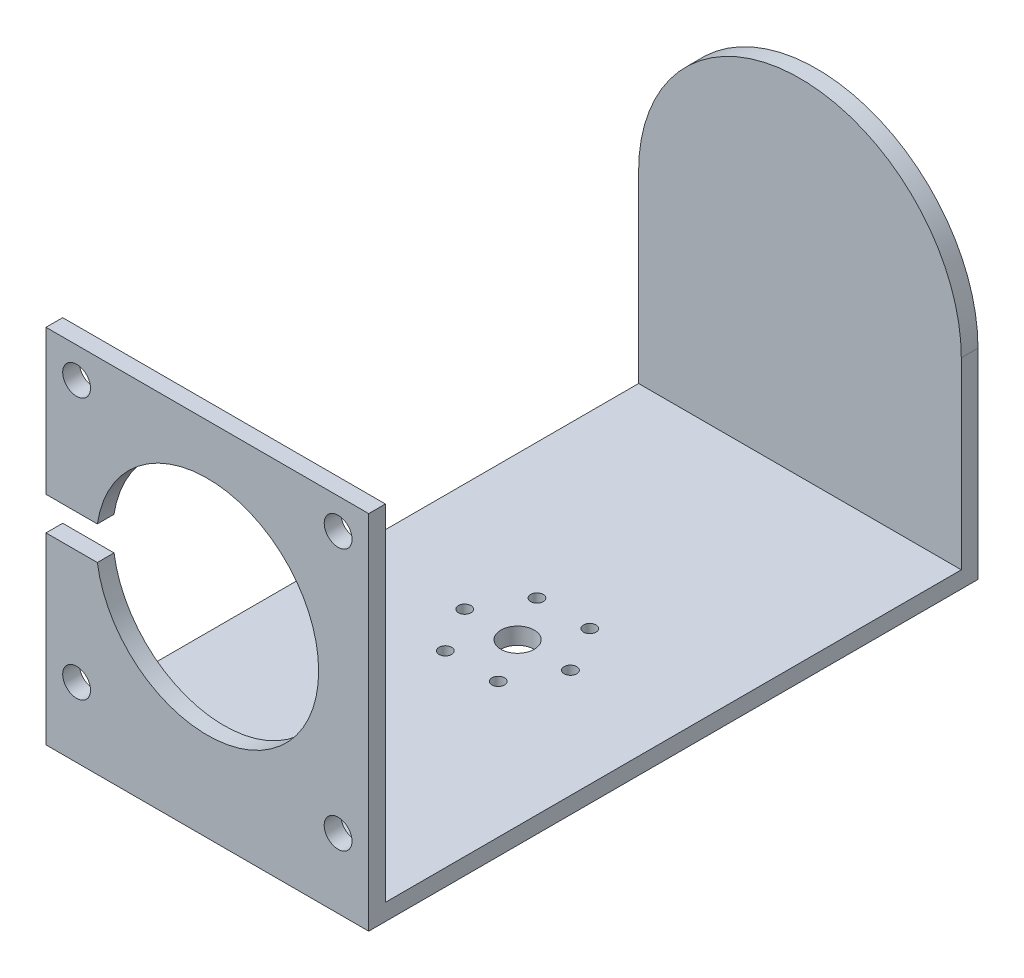
SolidWorks part; units mm, degrees
material "1060 Alloy"
ref_plane "Front Plane" through (0, 0, 0) normal (0, 0, 1) x (1, 0, 0)
ref_plane "Top Plane" through (0, 0, 0) normal (0, 1, 0) x (1, 0, 0)
ref_plane "Right Plane" through (0, 0, 0) normal (1, 0, 0) x (0, 0, -1)
sketch "Sketch1" plane through (0, 0, 0) normal (1, 0, 0) x (0, 0, -1)
  line L0 (-73.3517, 30.4008) -> (-73.3517, -29.5992)
  line L1 (-73.3517, -29.5992) -> (30.1483, -29.5992)
  line L2 (30.1483, -29.5992) -> (30.1483, 30.4008)
  line L3 (30.1483, 30.4008) -> (33.1483, 30.4008)
  line L4 (33.1483, 30.4008) -> (33.1483, -34.5992)
  line L5 (33.1483, -34.5992) -> (-76.3517, -34.5992)
  line L6 (-76.3517, -34.5992) -> (-76.3517, 30.4008)
  line L7 (-76.3517, 30.4008) -> (-73.3517, 30.4008)
  dimension "D1" = 60
  dimension "D2" = 103.5
  dimension "D3" = 3
  dimension "D4" = 65
  dimension "D5" = 109.5
extrude "Boss-Extrude1" add sketch "Sketch1" along normal blind 58
sketch "Sketch2" plane through (0, 0, 76.3517) normal (0, 0, 1) x (1, 0, 0)
  line L0 (0, 30.4008) -> (0, 24.9008) construction
  line L1 (0, 30.4008) -> (0, -34.5992) construction
  line L2 (0, 24.9008) -> (5.5, 24.9008) construction
  line L3 (29, 30.4008) -> (29, -34.5992) construction
  line L4 (58, 30.4008) -> (0, 30.4008) construction
  line L5 (58, -34.5992) -> (0, -34.5992) construction
  line L6 (58, 30.4008) -> (58, 1.4008) construction
  line L7 (58, 30.4008) -> (58, -34.5992) construction
  line L8 (58, 1.4008) -> (0, 1.4008) construction
  circle A0 centre (5.5, 24.9008) radius 2.5
  circle A1 centre (52.5, 24.9008) radius 2.5
  circle A2 centre (52.5, -22.0992) radius 2.5
  circle A3 centre (5.5, -22.0992) radius 2.5
  circle A4 centre (29, 1.4008) radius 20
  dimension "D4" = 5
  dimension "D5" = 40
  dimension "D1" = 5.5
  dimension "D2" = 5.5
  dimension "D3" = 29
extrude "Cut-Extrude1" cut sketch "Sketch2" against normal blind 58
sketch "Sketch3" plane through (0, 0, -33.1483) normal (0, 0, -1) x (-1, 0, 0)
  line L0 (-29, 30.4008) -> (-58, 30.4008)
  line L1 (-58, 30.4008) -> (0, 30.4008) construction
  line L2 (-58, 30.4008) -> (-58, 1.4008)
  line L3 (-58, -34.5992) -> (-58, 30.4008) construction
  arc A0 (-58, 1.4008) -> (-29, 30.4008) centre (-29, 1.4008) cw
  dimension "D1" = 29
extrude "Cut-Extrude2" cut sketch "Sketch3" against normal blind 58
sketch "Sketch4" plane through (0, 0, -33.1483) normal (0, 0, -1) x (-1, 0, 0)
  line L0 (-29, 30.4008) -> (0, 30.4008)
  line L1 (-29, 30.4008) -> (0, 30.4008) construction
  line L2 (0, 30.4008) -> (0, 1.4008)
  line L3 (0, -34.5992) -> (0, 30.4008) construction
  arc A0 (0, 1.4008) -> (-29, 30.4008) centre (-29, 1.4008) ccw
  arc A1 (-29, 30.4008) -> (-58, 1.4008) centre (-29, 1.4008) ccw construction
  dimension "D1" = 29
extrude "Cut-Extrude3" cut sketch "Sketch4" against normal blind 58
sketch "Sketch5" plane through (0, 0, -33.1483) normal (0, 0, -1) x (-1, 0, 0)
  circle A0 centre (-29, 1.4008) radius 2.95
  dimension "D1" = 5.9
extrude "Boss-Extrude2" add sketch "Sketch5" along normal blind 8
sketch "Sketch7" plane through (0, 0, 76.3517) normal (0, 0, 1) x (1, 0, 0)
  line L0 (29, 1.4008) -> (29, 4.4008) construction
  line L1 (29, 4.4008) -> (0, 4.4008)
  line L2 (0, 30.4008) -> (0, -34.5992) construction
  line L3 (29, 4.4008) -> (29, -1.5992)
  line L4 (29, -1.5992) -> (0, -1.5992)
  line L5 (0, -1.5992) -> (0, 4.4008)
  dimension "D1" = 3
  dimension "D2" = 6
extrude "Cut-Extrude5" cut sketch "Sketch7" against normal blind 10
sketch "Sketch13" plane through (0, -34.5992, 0) normal (0, -1, 0) x (-1, 0, 0)
  line L0 (-29, 33.1483) -> (-29, -20.6017) construction
  line L1 (-58, 33.1483) -> (0, 33.1483) construction
  dimension "D1" = 53.75
sketch "Sketch18" plane through (34.226, -34.5992, 37.4771) normal (0, -1, 0) x (-1, 0, 0)
  line L0 (5.226, 16.8754) -> (14.726, 16.8754) construction
  circle A0 centre (5.226, 16.8754) radius 9.5
  dimension "D1" = 19
hole_wizard "#4-40 Tapped Hole4" positions "Sketch24" profile "Sketch23" tap size "#4-40" standard "ANSI Inch"
sketch "Sketch24" plane through (0, -34.5992, 0) normal (0, -1, 0) x (-1, 0, 0)
  point P0 (-19.5, -20.6017)
  point P8 (-24.25, -28.8289)
  point P9 (-33.75, -28.8289)
  point P10 (-38.5, -20.6017)
  point P11 (-33.75, -12.3744)
  point P12 (-24.25, -12.3744)
  dimension "D1" = 6
sketch "Sketch23" plane through (19.5, -34.5992, 20.6017) normal (1, 0, 0) x (0, 0, -1)
  line L0 (0, 0) -> (0, 8.2792)
  line L1 (0, 8.2792) -> (1.1303, 7.6)
  line L2 (1.1303, 7.6) -> (1.1303, 0)
  line L5 (1.1303, 0) -> (0, 0)
  line L10 (0, 8.2792) -> (-1.1303, 7.6) construction
  line L11 (0, -6.35) -> (0, 107.95) construction
  dimension "Tap Drill Dia." = 2.2606
  dimension "Tap Drill Depth" = 7.6
  dimension "Drill Angle" = 118
cosmetic thread "Hole Thread19" parameters "D1"=3, "D2"=2.8448
cosmetic thread "Hole Thread20" parameters "D1"=3, "D2"=2.8448
cosmetic thread "Hole Thread21" parameters "D1"=3, "D2"=2.8448
cosmetic thread "Hole Thread22" parameters "D1"=3, "D2"=2.8448
cosmetic thread "Hole Thread23" parameters "D1"=3, "D2"=2.8448
cosmetic thread "Hole Thread24" parameters "D1"=3, "D2"=2.8448
sketch "Sketch25" plane through (0, -34.5992, 0) normal (0, -1, 0) x (1, 0, 0)
  circle A0 centre (29, 20.6017) radius 3
  dimension "D1" = 6
extrude "Cut-Extrude6" cut sketch "Sketch25" against normal blind 10
sketch "Sketch26" plane through (58, 0, 0) normal (1, 0, 0) x (0, 0, -1)
  line L0 (-73.3517, -29.5992) -> (-73.3517, -31.5992)
  line L1 (-73.3517, -31.5992) -> (30.1483, -31.5992)
  line L2 (30.1483, -31.5992) -> (30.1483, -29.5992)
  line L3 (30.1483, -29.5992) -> (-73.3517, -29.5992)
  dimension "D1" = 2
extrude "Cut-Extrude7" cut sketch "Sketch26" against normal blind 90
